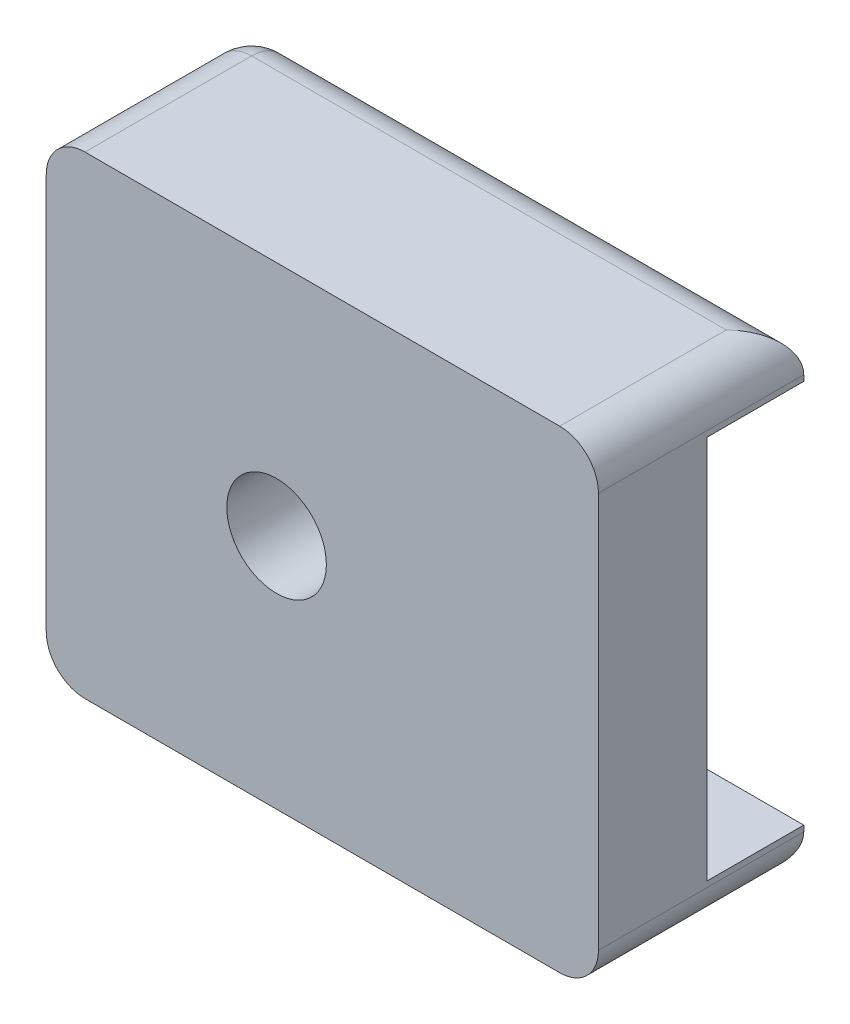
SolidWorks part; units mm, degrees
ref_plane "Front Plane" through (0, 0, 0) normal (0, 0, 1) x (1, 0, 0)
ref_plane "Top Plane" through (0, 0, 0) normal (0, 1, 0) x (1, 0, 0)
ref_plane "Right Plane" through (0, 0, 0) normal (1, 0, 0) x (0, 0, -1)
sketch "Sketch1" plane through (0, 0, 0) normal (0, 0, 1) x (1, 0, 0)
  line L0 (-63.5, 5.2496) -> (-63.5, -19.4278) construction
  line L1 (-66.675, 8.4246) -> (-30.48, 8.4246)
  line L2 (-66.675, 8.4246) -> (-66.675, -22.6028)
  line L3 (-66.675, -22.6028) -> (-30.48, -22.6028)
  line L4 (-30.48, 8.4246) -> (-30.48, -22.6028)
  line L5 (-30.48, 5.2496) -> (-63.5, 5.2496) construction
  line L6 (-63.5, -19.4278) -> (-30.48, -19.4278) construction
  line L8 (-30.48, 5.2496) -> (-30.48, -19.4278) construction
  circle A0 centre (-51.5779, -7.0891) radius 3.2639
  dimension "D1" = 3.175
  dimension "D2" = 3.175
  dimension "D3" = 3.175
extrude "Boss-Extrude1" add sketch "Sketch1" along normal blind 7.1069
sketch "Sketch2" plane through (0, 0, 0) normal (0, 0, -1) x (-1, 0, 0)
  line L0 (30.48, -19.6818) -> (30.48, -22.6028)
  line L1 (30.48, -22.6028) -> (30.48, 8.4246) construction
  line L2 (30.48, -22.6028) -> (66.675, -22.6028)
  line L3 (66.675, -22.6028) -> (66.675, 8.4246)
  line L4 (66.675, 8.4246) -> (30.48, 8.4246)
  line L5 (30.48, 8.4246) -> (30.48, 5.5036)
  line L6 (30.48, 5.5036) -> (63.754, 5.5036)
  line L7 (63.754, 5.5036) -> (63.754, -19.6818)
  line L8 (63.754, -19.6818) -> (30.48, -19.6818)
  line L9 (63.5, 5.2496) -> (63.5, -19.4278) construction
  line L10 (44.7357, 5.2496) -> (63.5, 5.2496) construction
  line L11 (44.7357, -19.4278) -> (63.5, -19.4278) construction
  dimension "D1" = 0.254
  dimension "D2" = 0.254
  dimension "D3" = 0.254
extrude "Boss-Extrude3" add sketch "Sketch2" along normal up to surface (6.35 mm away)
fillet "Fillet1" radius 2.54 7 edges at (-66.675, -7.0891, -6.35) (-48.5775, 8.4246, -6.35) (-48.5775, -22.6028, -6.35) (-30.48, 8.4246, 0.3785) (-30.48, -22.6028, 0.3785) (-66.675, -22.6028, 0.3785) (-66.675, 8.4246, 0.3785)
